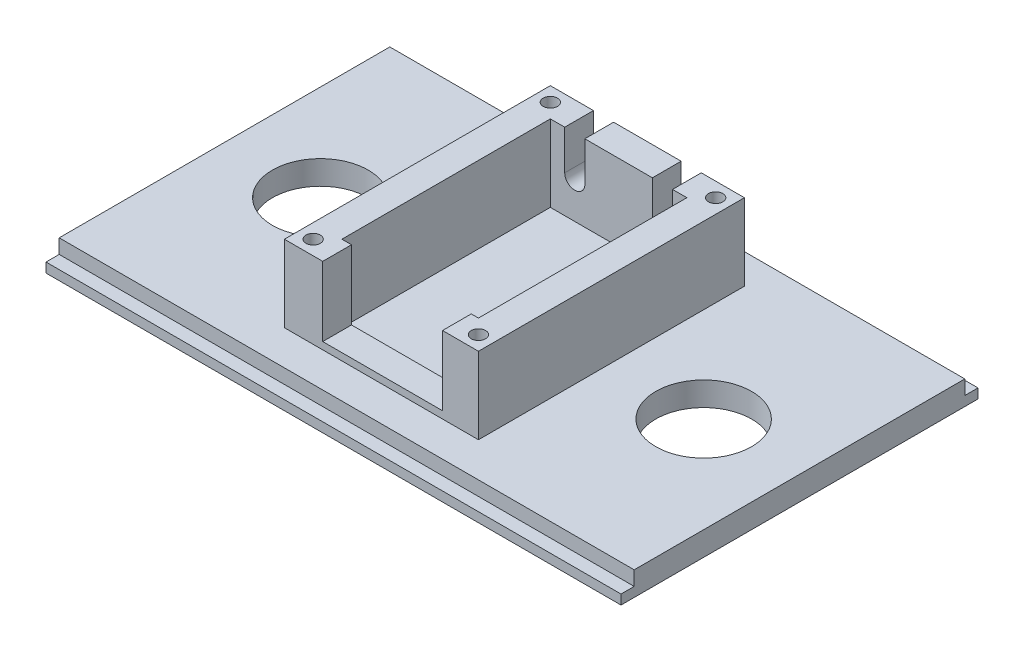
SolidWorks part; units mm, degrees
ref_plane "Front Plane" through (0, 0, 0) normal (0, 0, 1) x (1, 0, 0)
ref_plane "Top Plane" through (0, 0, 0) normal (0, 1, 0) x (1, 0, 0)
ref_plane "Right Plane" through (0, 0, 0) normal (1, 0, 0) x (0, 0, -1)
sketch "Sketch1" plane through (0, 0, 0) normal (0, 1, 0) x (1, 0, 0)
  line L1 (-60, -37.25) -> (60, -37.25)
  line L2 (-60, -37.25) -> (-60, 37.25)
  line L3 (-60, 37.25) -> (60, 37.25)
  line L4 (60, -37.25) -> (60, 37.25)
  line L5 (-60, -37.25) -> (60, 37.25) construction
  line L6 (-60, 37.25) -> (60, -37.25) construction
  point P0 (0, 0)
  dimension "D1" = 120
  dimension "D2" = 74.5
extrude "Boss-Extrude1" add sketch "Sketch1" along normal blind 2
sketch "Sketch2" plane through (0, 2, 0) normal (0, 1, 0) x (1, 0, 0)
  line L0 (-60, 37.25) -> (-60, -37.25) construction
  line L1 (-60, 34.5) -> (60, 34.5)
  line L2 (-60, 34.5) -> (-60, -34.5)
  line L3 (-60, -34.5) -> (60, -34.5)
  line L4 (60, 34.5) -> (60, -34.5)
  line L5 (60, -37.25) -> (60, 37.25) construction
  line L6 (-60, -37.25) -> (60, -37.25) construction
  line L7 (60, 37.25) -> (-60, 37.25) construction
  dimension "D1" = 2.75
  dimension "D2" = 2.75
extrude "Boss-Extrude2" add sketch "Sketch2" along normal blind 3
sketch "Sketch3" plane through (0, 5, 0) normal (0, 1, 0) x (1, 0, 0)
  line L0 (0, -1000) -> (0, 49000) construction
  line L1 (60, 37.25) -> (-60, 37.25) construction
  line L2 (14.25, -21.25) -> (-14.25, -21.25)
  line L3 (14.25, -21.25) -> (14.25, 22.25)
  line L4 (14.25, 22.25) -> (-14.25, 22.25)
  line L5 (-14.25, -21.25) -> (-14.25, 22.25)
  line L6 (14.25, -21.25) -> (-14.25, 22.25) construction
  line L7 (14.25, 22.25) -> (-14.25, -21.25) construction
  line L9 (-20.25, -27.25) -> (20.25, -27.25)
  line L10 (-20.25, -27.25) -> (-20.25, 28.25)
  line L11 (-20.25, 28.25) -> (20.25, 28.25)
  line L12 (20.25, -27.25) -> (20.25, 28.25)
  line L13 (-20.25, -27.25) -> (20.25, 28.25) construction
  line L14 (-20.25, 28.25) -> (20.25, -27.25) construction
  point P1 (0, 0.5)
  point P10 (0, 0.5)
  dimension "D1" = 28.5
  dimension "D2" = 43.5
  dimension "D3" = 15
  dimension "D4" = 6
  dimension "D5" = 6
extrude "Boss-Extrude3" add sketch "Sketch3" along normal blind 16
sketch "Sketch4" plane through (0, 0, 27.25) normal (0, 0, 1) x (1, 0, 0)
  line L0 (-20.25, 21) -> (20.25, 21) construction
  line L1 (-12.25, 21) -> (12.75, 21)
  line L2 (-12.25, 21) -> (-12.25, 6.5)
  line L3 (-12.25, 6.5) -> (12.75, 6.5)
  line L4 (12.75, 21) -> (12.75, 6.5)
  line L5 (20.25, 21) -> (20.25, 5) construction
  dimension "D1" = 25
  dimension "D2" = 14.5
  dimension "D3" = 7.5
extrude "Cut-Extrude1" cut sketch "Sketch4" against normal blind 16
sketch "Sketch5" plane through (0, 0, -28.25) normal (0, 0, -1) x (-1, 0, 0)
  line L0 (-20.25, 21) -> (20.25, 21) construction
  line L1 (-11.25, 21) -> (-7.05, 21)
  line L2 (-11.25, 21) -> (-11.25, 12.75)
  line L3 (-11.25, 12.75) -> (-7.05, 12.75)
  line L4 (-7.05, 21) -> (-7.05, 12.75)
  line L5 (-20.25, 21) -> (-20.25, 5) construction
  line L6 (7.05, 21) -> (11.25, 21)
  line L7 (7.05, 21) -> (7.05, 12.75)
  line L8 (7.05, 12.75) -> (11.25, 12.75)
  line L9 (11.25, 21) -> (11.25, 12.75)
  line L10 (20.25, 21) -> (20.25, 5) construction
  circle A0 centre (-9.15, 12.75) radius 2.1
  circle A1 centre (9.15, 12.75) radius 2.1
  line M7 (20.25, 21) -> (-20.25, 21)
  dimension "D1" = 4.2
  dimension "D2" = 4.2
  dimension "D3" = 8.25
  dimension "D4" = 8.25
  dimension "D5" = 9
  dimension "D6" = 9
extrude "Cut-Extrude2" cut sketch "Sketch5" against normal blind 16 contours A0 L4 L2 M7 | L3 A0 | L3 A0 | L8 A1 | L8 A1 | A1 L9 L7 M7
sketch "Sketch6" plane through (0, 21, 0) normal (0, 1, 0) x (1, 0, 0)
  line L0 (-1017.2446, 25.25) -> (48982.7554, 25.25) construction
  line L1 (-1016.2592, -24.25) -> (48983.7408, -24.25) construction
  line L2 (-17.25, -971.5464) -> (-17.25, 49028.4536) construction
  line L3 (17.25, -971.5464) -> (17.25, 49028.4536) construction
  line L4 (-20.25, 28.25) -> (-20.25, -27.25) construction
  line L5 (-11.25, 28.25) -> (-20.25, 28.25) construction
  line L6 (20.25, -27.25) -> (20.25, 28.25) construction
  line L7 (-20.25, -27.25) -> (20.25, -27.25) construction
  circle A1 centre (17.25, 25.25) radius 1.5
  circle A2 centre (17.25, -24.25) radius 1.5
  circle A3 centre (-17.25, -24.25) radius 1.5
  circle A4 centre (-17.25, 25.25) radius 1.5
  dimension "D6" = 3
  dimension "D8" = 3
  dimension "D10" = 3
  dimension "D12" = 3
  dimension "D1" = 3
  dimension "D2" = 3
  dimension "D3" = 3
  dimension "D4" = 3
  dimension "D5" = 0
  dimension "D7" = 0
  dimension "D9" = 0
  dimension "D11" = 0
extrude "Cut-Extrude3" cut sketch "Sketch6" against normal blind 10
sketch "Sketch7" plane through (0, 5, 0) normal (0, 1, 0) x (1, 0, 0)
  line L0 (-1000, 0) -> (49000, 0) construction
  line L1 (-60, 34.5) -> (-60, -34.5) construction
  line L2 (60, -34.5) -> (60, 34.5) construction
  circle A0 centre (-40, 0) radius 10
  circle A1 centre (40, 0) radius 10
  dimension "D1" = 20
  dimension "D2" = 20
  dimension "D3" = 20
  dimension "D4" = 20
extrude "Cut-Extrude4" cut sketch "Sketch7" against normal through all both and the other way through all
